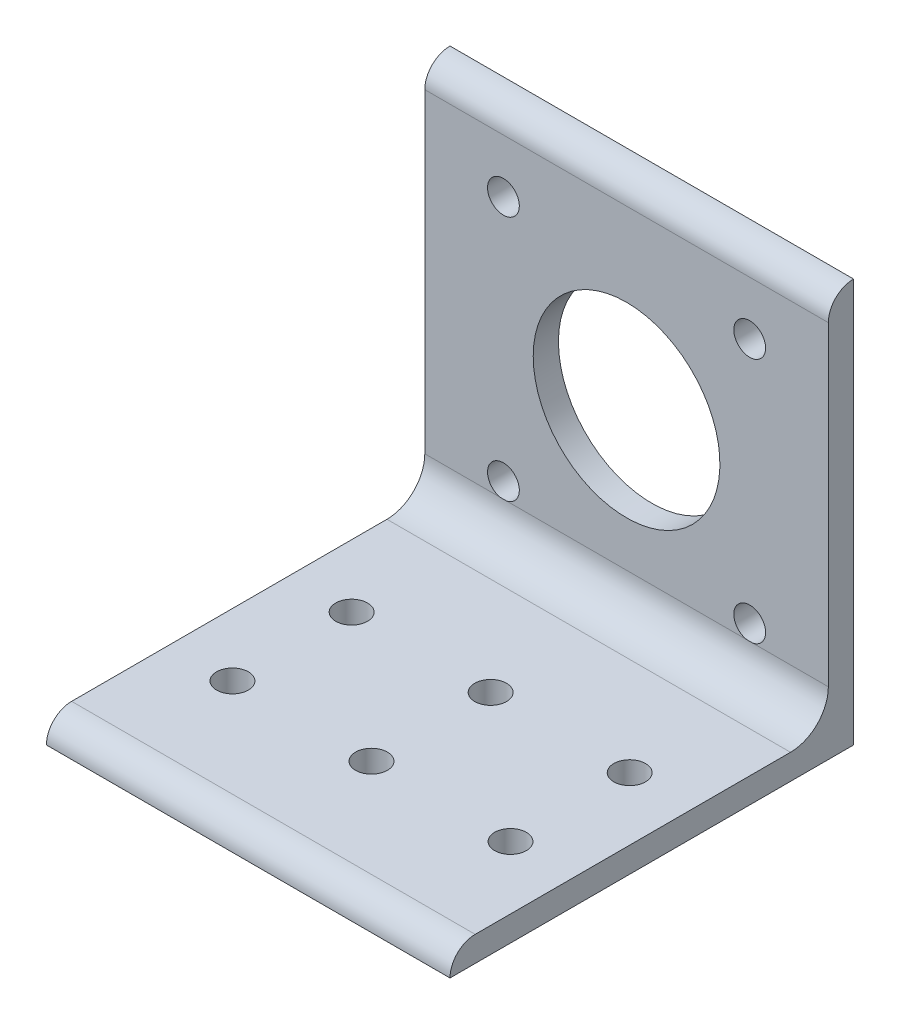
SolidWorks part; units mm, degrees
material "AISI 1020"
ref_plane "Alzado" through (0, 0, 0) normal (0, 0, 1) x (1, 0, 0)
ref_plane "Planta" through (0, 0, 0) normal (0, 1, 0) x (1, 0, 0)
ref_plane "Vista lateral" through (0, 0, 0) normal (1, 0, 0) x (0, 0, -1)
sketch "Croquis1" plane through (0, 0, 0) normal (0, 0, 1) x (1, 0, 0)
  line L0 (-25.4, 0) -> (25.4, 0)
  point P4 (0, 0)
  dimension "D1" = 50.8
other "Hierro angular 2 X 2 X 0.125(1)"
ref_plane "Plano1" through (-25.4, 0, 0) normal (1, 0, 0) x (0, 1, 0)
sketch "Sketch1" plane through (-25.4, 0, 0) normal (1, 0, 0) x (0, 1, 0)
  line L0 (0, 0) -> (0, 50.8)
  line L1 (0, 50.8) -> (0.0051, 50.8)
  line L2 (3.175, 47.6301) -> (3.175, 7.9375)
  line L3 (7.9375, 3.175) -> (47.6301, 3.175)
  line L4 (50.8, 0.0051) -> (50.8, 0)
  line L5 (50.8, 0) -> (0, 0)
  arc A0 (50.8, 0.0051) -> (47.6301, 3.175) centre (47.6301, 0.0051) ccw
  arc A1 (0.0051, 50.8) -> (3.175, 47.6301) centre (0.0051, 47.6301) cw
  arc A2 (7.9375, 3.175) -> (3.175, 7.9375) centre (7.9375, 7.9375) cw
  point P10 (25.4, 0)
  point P14 (0, 25.4)
  point P15 (3.175, 25.4)
  point P16 (25.4, 3.175)
  point P17 (3.175, 50.8)
  point P18 (50.8, 3.175)
  point P19 (0, 0)
  dimension "D2" = 0.0051
  dimension "Radius_1" = 4.7625
  dimension "D1" = 3.175
  dimension "H_leg" = 50.8
sketch "Croquis3" plane through (0, 0, 0) normal (0, 0, -1) x (-1, 0, 0)
  line L0 (-25.4, 0) -> (25.4, 50.8) construction
  line L2 (-15.5, 9.9) -> (15.5, 9.9) construction
  line L3 (-15.5, 9.9) -> (-15.5, 40.9) construction
  line L4 (-15.5, 40.9) -> (15.5, 40.9) construction
  line L5 (15.5, 9.9) -> (15.5, 40.9) construction
  line L6 (-15.5, 9.9) -> (15.5, 40.9) construction
  line L7 (-15.5, 40.9) -> (15.5, 9.9) construction
  circle A0 centre (0, 25.4) radius 11.75
  circle A1 centre (-15.5, 40.9) radius 2
  circle A2 centre (15.5, 40.9) radius 2
  circle A3 centre (15.5, 9.9) radius 2
  circle A4 centre (-15.5, 9.9) radius 2
  dimension "D1" = 23.5
  dimension "D4" = 4
  dimension "D2" = 31
  dimension "D3" = 31
extrude "Cortar-Extruir1" cut sketch "Croquis3" against normal up to surface (3.175 mm away) up to face at (0, 27.7838, 3.175)
sketch "Croquis4" plane through (0, 3.175, 0) normal (0, 1, 0) x (1, 0, 0)
  line L0 (-25.4, -47.6301) -> (25.4, -7.9375) construction
  line L2 (-17.5, -35.2838) -> (17.5, -35.2838) construction
  line L3 (-17.5, -35.2838) -> (-17.5, -20.2838) construction
  line L4 (-17.5, -20.2838) -> (17.5, -20.2838) construction
  line L5 (17.5, -35.2838) -> (17.5, -20.2838) construction
  line L6 (-17.5, -35.2838) -> (17.5, -20.2838) construction
  line L7 (-17.5, -20.2838) -> (17.5, -35.2838) construction
  circle A0 centre (-17.5, -20.2838) radius 2
  circle A1 centre (17.5, -20.2838) radius 2
  circle A2 centre (17.5, -35.2838) radius 2
  circle A3 centre (-17.5, -35.2838) radius 2
  circle A4 centre (0, -20.2838) radius 2
  circle A5 centre (0, -35.2838) radius 2
  point P4 (0, -27.7838)
  dimension "D3" = 4
  dimension "D1" = 15
  dimension "D2" = 35
extrude "Cortar-Extruir2" cut sketch "Croquis4" against normal up to surface (3.175 mm away) up to face at (0, 0, 25.4)
